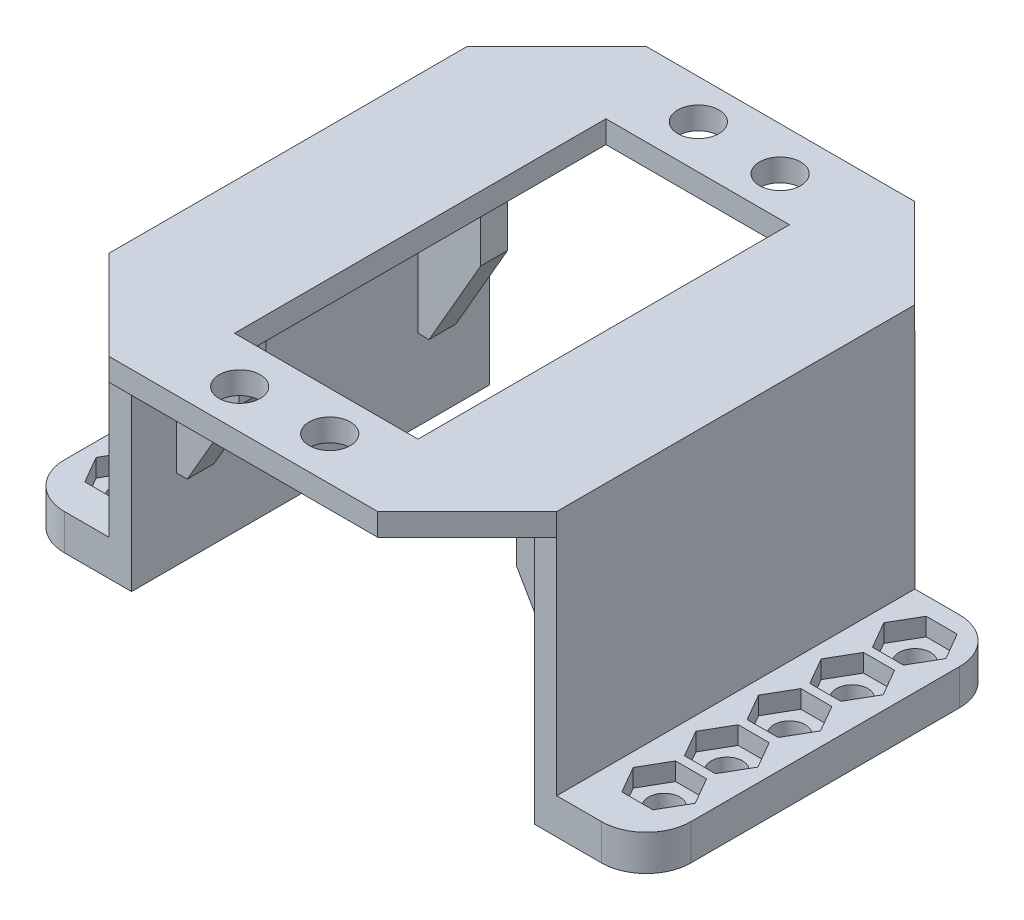
SolidWorks part; units mm, degrees
ref_plane "Front Plane" through (0, 0, 0) normal (0, 0, 1) x (1, 0, 0)
ref_plane "Top Plane" through (0, 0, 0) normal (0, 1, 0) x (1, 0, 0)
ref_plane "Right Plane" through (0, 0, 0) normal (1, 0, 0) x (0, 0, -1)
sketch "Sketch1" plane through (0, 0, 0) normal (0, 1, 0) x (1, 0, 0)
  line L1 (-25, 30) -> (25, 30)
  line L2 (-25, 30) -> (-25, -30)
  line L3 (-25, -30) -> (25, -30)
  line L4 (25, 30) -> (25, -30)
  line L5 (-25, 30) -> (25, -30) construction
  line L6 (-25, -30) -> (25, 30) construction
  point P0 (0, 0)
  dimension "D1" = 50
  dimension "D2" = 60
extrude "Boss-Extrude1" add sketch "Sketch1" along normal blind 2.5
sketch "Sketch2" plane through (0, 2.5, 0) normal (0, 1, 0) x (1, 0, 0)
  line L1 (-10.25, 20.75) -> (10.25, 20.75)
  line L2 (-10.25, 20.75) -> (-10.25, -20.75)
  line L3 (-10.25, -20.75) -> (10.25, -20.75)
  line L4 (10.25, 20.75) -> (10.25, -20.75)
  line L5 (-10.25, 20.75) -> (10.25, -20.75) construction
  line L6 (-10.25, -20.75) -> (10.25, 20.75) construction
  point P0 (0, 0)
  dimension "D1" = 41.5
  dimension "D2" = 20.5
extrude "Cut-Extrude1" cut sketch "Sketch2" against normal through all
chamfer "Chamfer1" distance 10 angle 45 4 edges at (-25, 1.25, -30) (-25, 1.25, 30) (25, 1.25, 30) (25, 1.25, -30)
sketch "Sketch3" plane through (0, 0, 0) normal (0, -1, 0) x (1, 0, 0)
  line L1 (-25, 20) -> (-22.5, 20)
  line L2 (-25, 20) -> (-25, -20.0083)
  line L3 (-25, -20.0083) -> (-22.5, -20.0083)
  line L4 (-22.5, 20) -> (-22.5, -20.0083)
  dimension "D1" = 2.5
extrude "Boss-Extrude2" add sketch "Sketch3" along normal blind 29
sketch "Sketch4" plane through (-25, 0, 0) normal (-1, 0, 0) x (0, 0, 1)
  line L0 (20, -29) -> (20, 0) construction
  line L1 (-20.0083, -29) -> (20, -29)
  line L2 (-20.0083, -29) -> (-20.0083, -25)
  line L3 (-20.0083, -25) -> (20, -25)
  line L4 (20, -29) -> (20, -25)
  dimension "D1" = 4
extrude "Boss-Extrude3" add sketch "Sketch4" along normal blind 10
sketch "Sketch5" plane through (0, -25, 0) normal (0, 1, 0) x (1, 0, 0)
  line L0 (-25, -20) -> (-25, 20.0083) construction
  line L1 (-35, 20.0083) -> (-25, 20.0083) construction
  circle A0 centre (-30, 15.0083) radius 1.75
  dimension "D2" = 3.5
  dimension "D1" = 5
  dimension "D3" = 5
extrude "Cut-Extrude2" cut sketch "Sketch5" against normal through all
sketch "Sketch6" plane through (0, -25, 0) normal (0, 1, 0) x (1, 0, 0)
  line L1 (-26.5359, 15.0083) -> (-28.2679, 18.0083)
  line L2 (-28.2679, 18.0083) -> (-31.7321, 18.0083)
  line L3 (-31.7321, 18.0083) -> (-33.4641, 15.0083)
  line L4 (-33.4641, 15.0083) -> (-31.7321, 12.0083)
  line L5 (-31.7321, 12.0083) -> (-28.2679, 12.0083)
  line L6 (-28.2679, 12.0083) -> (-26.5359, 15.0083)
  circle A0 centre (-30, 15.0083) radius 3 construction
  dimension "D1" = 6
extrude "Cut-Extrude3" cut sketch "Sketch6" against normal blind 2
pattern_linear "LPattern1" count 5 spacing 7 along (0, 0, 1) of "Cut-Extrude2", "Cut-Extrude3"
fillet "Fillet1" radius 5 2 edges at (-35, -27, -20.0083) (-35, -27, 20)
sketch "Sketch7" plane through (0, 0, 0) normal (0, -1, 0) x (1, 0, 0)
  line L0 (-22.5, -20.0083) -> (-22.5, 20) construction
  line L1 (-22.5, 15) -> (-15.5, 15)
  line L2 (-22.5, 15) -> (-22.5, 12)
  line L3 (-22.5, 12) -> (-15.5, 12)
  line L4 (-15.5, 15) -> (-15.5, 12)
  line L5 (-22.5, -20.0083) -> (-22.5, 20) construction
  line L6 (-22.5, -12.0083) -> (-15.5, -12.0083)
  line L7 (-22.5, -12.0083) -> (-22.5, -15.0083)
  line L8 (-22.5, -15.0083) -> (-15.5, -15.0083)
  line L9 (-15.5, -12.0083) -> (-15.5, -15.0083)
  line L10 (-22.5, 20) -> (-25, 20) construction
  line L11 (-30, -20.0083) -> (-22.5, -20.0083) construction
  dimension "D1" = 7
  dimension "D2" = 7
  dimension "D3" = 3
  dimension "D4" = 3
  dimension "D5" = 5
  dimension "D6" = 5
extrude "Boss-Extrude4" add sketch "Sketch7" along normal blind 20
chamfer "Chamfer2" distance 10 angle 30 2 edges at (-15.5, -20, -13.5083) (-15.5, -20, 13.5)
mirror "Mirror1" about plane through (0, 0, 0) normal (1, 0, 0) of "Chamfer2", "Boss-Extrude4", "Fillet1", "LPattern1", "Cut-Extrude3", "Cut-Extrude2", "Boss-Extrude3", "Boss-Extrude2"
sketch "Sketch8" plane through (0, 2.5, 0) normal (0, 1, 0) x (1, 0, 0)
  circle A0 centre (-4.8, 25.62) radius 2.3
  circle A1 centre (4.8, 25.1564) radius 2.3
  dimension "D4" = 4.6
  dimension "D5" = 4.6
  dimension "D1" = 4.8
  dimension "D2" = 4.8
  dimension "D3" = 25.62
extrude "Cut-Extrude4" cut sketch "Sketch8" against normal through all
mirror "Mirror2" about plane through (0, 0, 0) normal (0, 0, 1) of "Cut-Extrude4"
